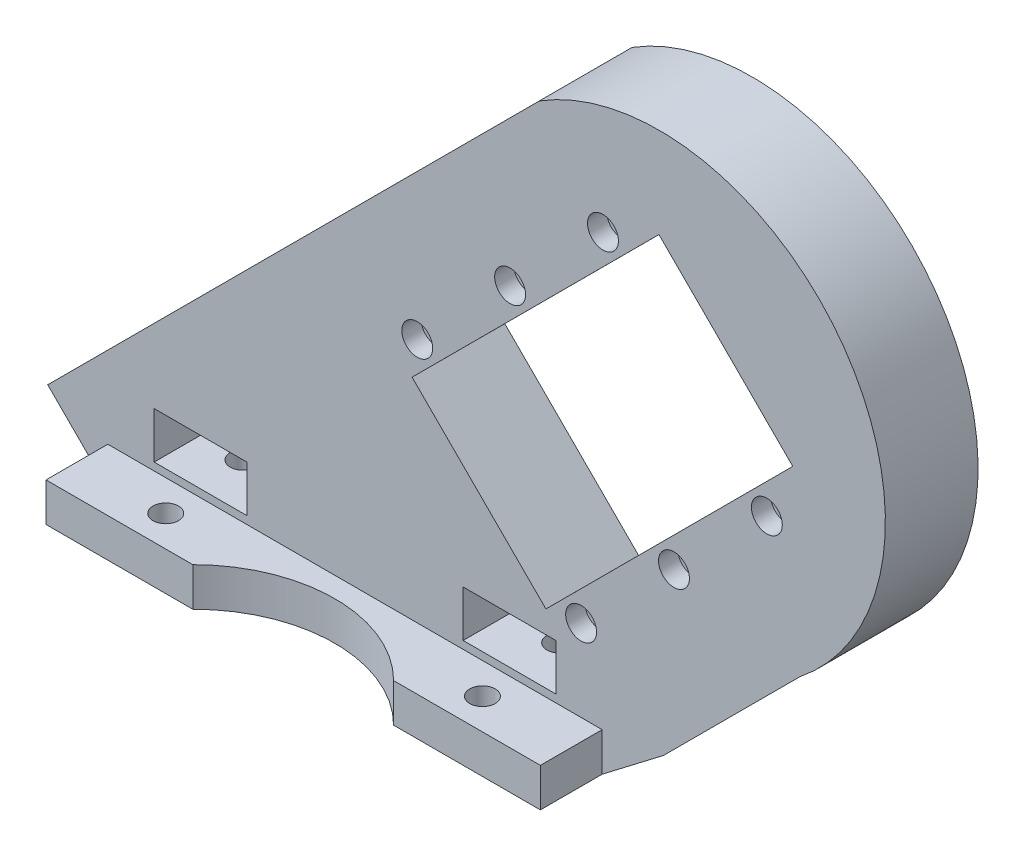
SolidWorks part; units mm, degrees
ref_plane "Front Plane" through (0, 0, 0) normal (0, 0, 1) x (1, 0, 0)
ref_plane "Top Plane" through (0, 0, 0) normal (0, 1, 0) x (1, 0, 0)
ref_plane "Right Plane" through (0, 0, 0) normal (1, 0, 0) x (0, 0, -1)
sketch "Sketch1" plane through (0, 0, 0) normal (0, 0, 1) x (1, 0, 0)
  line L0 (0, 0) -> (64, 0)
  line L1 (0, 0) -> (-7.7782, 7.7782)
  line L2 (-7.7782, 7.7782) -> (55.8614, 71.4178)
  line L3 (64, 0) -> (71.9419, 6.0766)
  line L4 (71.9419, 6.0766) -> (89.6196, 23.7543)
  arc A0 (89.6196, 23.7543) -> (55.8614, 71.4178) centre (71.415, 46.6472) ccw
  dimension "D1" = 64
  dimension "D2" = 90
  dimension "D3" = 11
  dimension "D4" = 10
  dimension "D5" = 25
extrude "Boss-Extrude2" add sketch "Sketch1" along normal blind 12
sketch "Sketch2" plane through (0, 0, 12) normal (0, 0, 1) x (1, 0, 0)
  line L0 (56.7185, 14.8894) -> (39.3917, 32.2109)
  line L1 (39.3917, 32.2109) -> (71.3481, 64.177)
  line L3 (56.7185, 14.8894) -> (88.6748, 46.8555)
  line L4 (88.6748, 46.8555) -> (71.3481, 64.177)
  circle A0 centre (71.415, 46.6472) radius 2.3395
  arc A2 (89.6196, 23.7543) -> (55.8614, 71.4178) centre (71.415, 46.6472) ccw construction
  dimension "D1" = 24.5
  dimension "D2" = 45.2
  dimension "D3" = 12.35
  dimension "D4" = 45.2
  dimension "D5" = 0
extrude "Cut-Extrude1" cut sketch "Sketch2" against normal through all contours L3 L4 L1 L0 A0
sketch "Sketch3" plane through (0, 0, 12) normal (0, 0, 1) x (1, 0, 0)
  line L0 (88.6748, 46.8555) -> (71.3481, 64.177) construction
  line L1 (56.7185, 14.8894) -> (88.6748, 46.8555) construction
  line L3 (39.3917, 32.2109) -> (56.7185, 14.8894) construction
  line L4 (48.0551, 23.5501) -> (80.0115, 55.5162)
  circle A0 centre (85.3172, 39.6071) radius 1.25
  circle A1 centre (73.2964, 27.5863) radius 1.25
  circle A2 centre (61.2756, 15.5655) radius 1.25
  circle A3 centre (64.1008, 60.8171) radius 1.25
  circle A4 centre (52.0836, 48.7926) radius 1.25
  circle A5 centre (40.0664, 36.7682) radius 1.25
  dimension "D1" = 2.5
  dimension "D2" = 7.5
  dimension "D3" = 2.75
  dimension "D4" = 3
extrude "Cut-Extrude2" cut sketch "Sketch3" against normal through all contours A4 | A5 | A3 | A0 | A1 | A2
sketch "Sketch5" plane through (0, 0, 0) normal (0, -1, 0) x (1, 0, 0)
  line L0 (0, 12) -> (0, 0) construction
  line L1 (0, 12) -> (64, 12) construction
  circle A0 centre (11.5, 6) radius 1.65
  circle A1 centre (52.5, 6) radius 1.65
  dimension "D1" = 3.3
  dimension "D2" = 11.5
  dimension "D4" = 6
  dimension "D3" = 2
extrude "Cut-Extrude3" cut sketch "Sketch5" against normal blind 6
sketch "Sketch6" plane through (0, 0, 12) normal (0, 0, 1) x (1, 0, 0)
  line L0 (0, 0) -> (64, 0) construction
  line L1 (18, 12) -> (6, 12)
  line L2 (18, 12) -> (18, 6)
  line L3 (18, 6) -> (6, 6)
  line L4 (6, 12) -> (6, 6)
  line L5 (12, 6) -> (12, 12) construction
  line L6 (18, 9) -> (6, 9) construction
  line L7 (58, 12) -> (58, 6)
  line L8 (58, 12) -> (46, 12)
  line L9 (46, 12) -> (46, 6)
  line L10 (58, 6) -> (46, 6)
  point P0 (12, 9)
  dimension "D1" = 6
  dimension "D2" = 12
  dimension "D3" = 12
  dimension "D4" = 6
  dimension "D5" = 2
extrude "Cut-Extrude4" cut sketch "Sketch6" against normal through all
sketch "Sketch8" plane through (0, 0, 0) normal (0, -1, 0) x (1, 0, 0)
  line L0 (0, 12) -> (0, 20)
  line L1 (0, 20) -> (64, 20)
  line L2 (64, 20) -> (64, 12)
  line L3 (0, 12) -> (64, 12)
  dimension "D1" = 8
  dimension "D2" = 64
extrude "Boss-Extrude3" add sketch "Sketch8" against normal blind 5
sketch "Sketch9" plane through (0, 0, 0) normal (0, -1, 0) x (1, 0, 0)
  line L0 (0, 20) -> (0, 12) construction
  circle A0 centre (11.5, 16) radius 1.65
  circle A2 centre (11.5, 6) radius 1.65 construction
  circle A3 centre (52.5, 16) radius 1.65
  dimension "D1" = 3.3
  dimension "D2" = 10
  dimension "D4" = 11.5
  dimension "D3" = 2
extrude "Cut-Extrude5" cut sketch "Sketch9" against normal blind 5
sketch "Sketch10" plane through (0, 0, 12) normal (0, 0, 1) x (1, 0, 0)
  line L1 (80.0115, 55.5162) -> (69.52, 45.0248)
  line L2 (88.6748, 46.8555) -> (71.3481, 64.177) construction
  circle A0 centre (85.3172, 39.6071) radius 2
  circle A1 centre (73.2964, 27.5863) radius 2
  circle A2 centre (61.2756, 15.5655) radius 2
  circle A3 centre (40.0607, 36.7803) radius 2
  circle A4 centre (52.0816, 48.8011) radius 2
  circle A5 centre (64.1024, 60.8219) radius 2
  point P4 (60.828, 15.1153)
  dimension "D1" = 4
  dimension "D2" = 3
extrude "Cut-Extrude6" cut sketch "Sketch10" against normal blind 2.5 contours A1 | A2 | A0 | A4 | A3 | A5
sketch "Sketch11" plane through (0, 5, 0) normal (0, 1, 0) x (1, 0, 0)
  line L0 (64, -20) -> (0, -20) construction
  arc A0 (19, -20) -> (45, -20) centre (32, -33) cw
  point P0 (19, -20)
  point P1 (32, -20)
  point P4 (45, -20)
  line M6 (0, -20) -> (64, -20)
  dimension "D1" = 13
  dimension "D2" = 13
extrude "Cut-Extrude7" cut sketch "Sketch11" against normal blind 10 and the other way through all contours A0 M6
